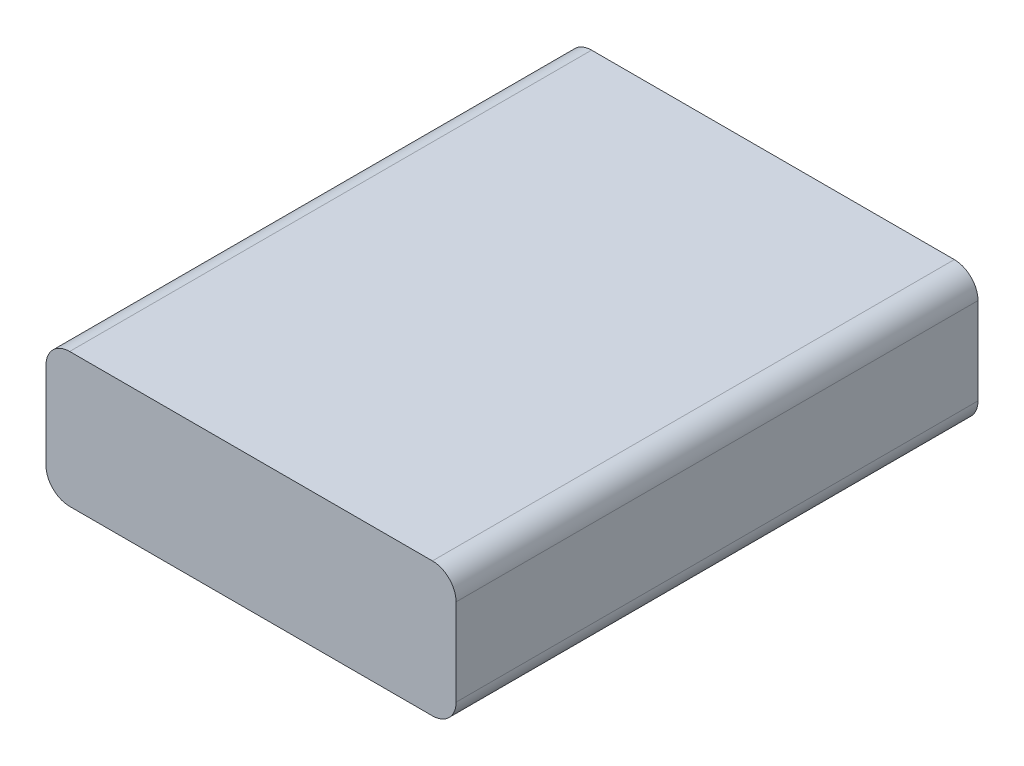
SolidWorks part; units mm, degrees
ref_plane "Front Plane" through (0, 0, 0) normal (0, 0, 1) x (1, 0, 0)
ref_plane "Top Plane" through (0, 0, 0) normal (0, 1, 0) x (1, 0, 0)
ref_plane "Right Plane" through (0, 0, 0) normal (1, 0, 0) x (0, 0, -1)
sketch "Sketch1" plane through (0, 0, 0) normal (0, 0, 1) x (1, 0, 0)
  line L1 (-24.325, 0) -> (24.325, 0)
  line L2 (-27.5, 3.175) -> (-27.5, 14.825)
  line L3 (-24.325, 18) -> (24.325, 18)
  line L4 (27.5, 3.175) -> (27.5, 14.825)
  arc A0 (24.325, 18) -> (27.5, 14.825) centre (24.325, 14.825) cw
  arc A1 (24.325, 0) -> (27.5, 3.175) centre (24.325, 3.175) ccw
  arc A2 (-24.325, 0) -> (-27.5, 3.175) centre (-24.325, 3.175) cw
  arc A3 (-27.5, 14.825) -> (-24.325, 18) centre (-24.325, 14.825) cw
  point P7 (27.5, 18)
  point P10 (27.5, 0)
  point P13 (-27.5, 0)
  point P16 (0, 0)
  dimension "D3" = 3.175
  dimension "D1" = 55
  dimension "D2" = 18
extrude "Boss-Extrude1" add sketch "Sketch1" along normal blind 70
